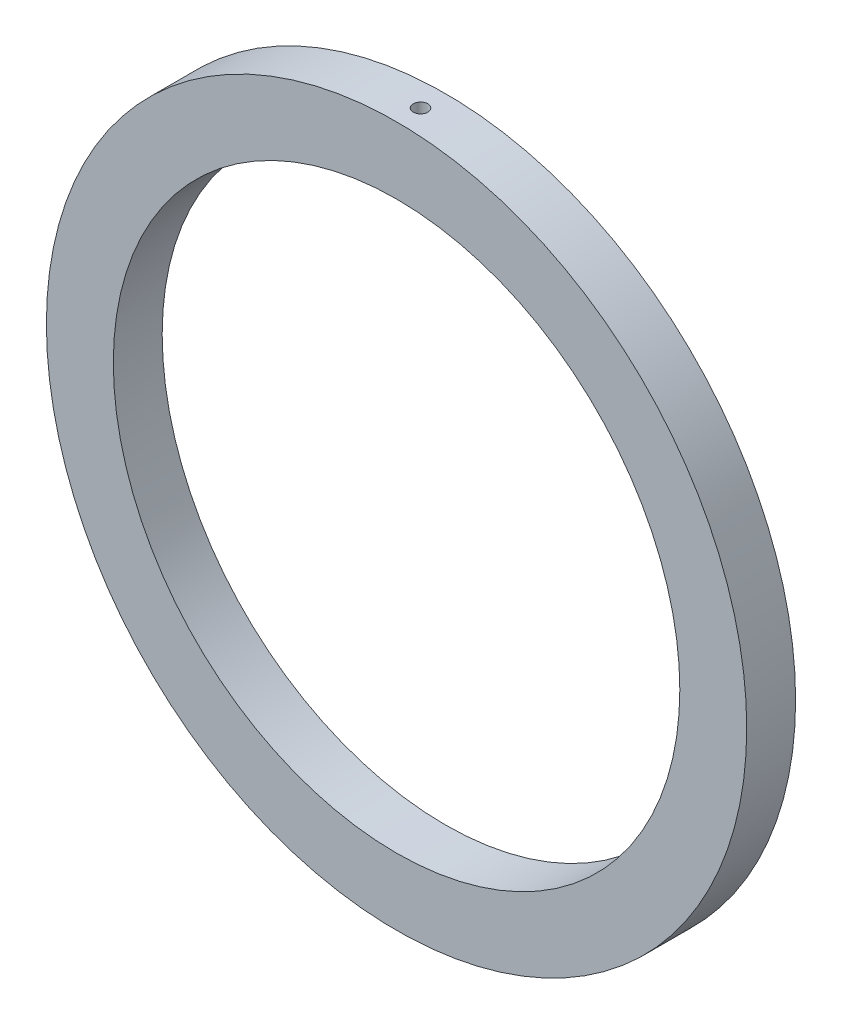
SolidWorks part; units mm, degrees
ref_plane "Front Plane" through (0, 0, 0) normal (0, 0, 1) x (1, 0, 0)
ref_plane "Top Plane" through (0, 0, 0) normal (0, 1, 0) x (1, 0, 0)
ref_plane "Right Plane" through (0, 0, 0) normal (1, 0, 0) x (0, 0, -1)
sketch "Sketch1" plane through (0, 0, 0) normal (0, 0, 1) x (1, 0, 0)
  circle A0 centre (0, 0) radius 28.575
  circle A1 centre (0, 0) radius 23.114
  dimension "D1" = 57.15
  dimension "D2" = 46.228
extrude "Boss-Extrude1" add sketch "Sketch1" along normal blind 1.9939 and the other way blind 1.9939
sketch "Sketch2" plane through (0, 0, 1.9939) normal (0, 0, 1) x (1, 0, 0)
  circle A0 centre (0, 0) radius 24.384
  circle A1 centre (0, 0) radius 23.114
  dimension "D1" = 46.228
  dimension "D2" = 48.768
extrude "Cut-Extrude1" [suppressed] cut sketch "Sketch2" against normal blind 0.8128 flip side to cut
mirror "Mirror1" [suppressed] about plane through (0, 0, 0) normal (0, 0, 1)
hole_wizard "#0-80 Tapped Hole1" positions "3DSketch2" profile "Sketch3" tap size "#0-80" standard "ANSI Inch"
sketch3d "3DSketch2"
  point P0 (0, 28.575, 0.0419)
sketch "Sketch3" plane through (0, 28.575, 0.0419) normal (1, 0, 0) x (0, 0, 1)
  line L0 (0, 0) -> (0, 4.4219)
  line L1 (0, 4.4219) -> (0.5956, 4.064)
  line L2 (0.5956, 4.064) -> (0.5956, 0)
  line L5 (0.5956, 0) -> (0, 0)
  line L10 (0, 4.4219) -> (-0.5956, 4.064) construction
  line L11 (0, -6.35) -> (0, 107.95) construction
  dimension "Tap Drill Dia." = 1.1913
  dimension "Tap Drill Depth" = 4.064
  dimension "Drill Angle" = 118
